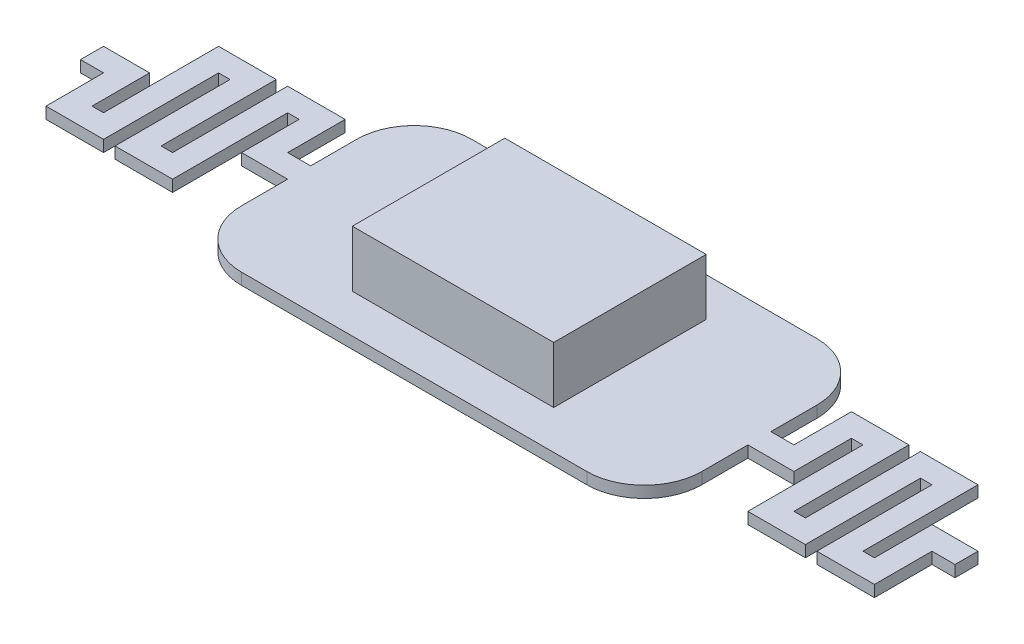
SolidWorks part; units mm, degrees
ref_plane "Front Plane" through (0, 0, 0) normal (0, 0, 1) x (1, 0, 0)
ref_plane "Top Plane" through (0, 0, 0) normal (0, 1, 0) x (1, 0, 0)
ref_plane "Right Plane" through (0, 0, 0) normal (1, 0, 0) x (0, 0, -1)
sketch "Sketch1" plane through (0, 0, 0) normal (0, 1, 0) x (1, 0, 0)
  line L1 (-4, 2) -> (4, 2)
  line L2 (-4, 2) -> (-4, -2)
  line L3 (-4, -2) -> (4, -2)
  line L4 (4, 2) -> (4, -2)
  line L5 (-4, 2) -> (4, -2) construction
  line L6 (-4, -2) -> (4, 2) construction
  point P0 (0, 0)
  dimension "D1" = 8
  dimension "D2" = 4
extrude "Boss-Extrude1" add sketch "Sketch1" along normal blind 0.2
fillet "Fillet1" radius 1 4 edges at (4, 0.1, -2) (4, 0.1, 2) (-4, 0.1, 2) (-4, 0.1, -2)
sketch "Sketch2" plane through (0, 0.2, 0) normal (0, 1, 0) x (1, 0, 0)
  line L0 (4, 0) -> (4.6, 0)
  line L1 (4, -1) -> (4, 1) construction
  line L2 (4.6, 0) -> (4.6, 1)
  line L3 (4.6, 1) -> (5.2, 1)
  line L4 (5.2, 1) -> (5.2, -1)
  line L5 (5.2, -1) -> (5.8, -1)
  line L6 (5.8, -1) -> (5.8, 1)
  line L7 (5.8, 1) -> (6.4, 1)
  line L8 (6.4, 1) -> (6.4, -1)
  line L9 (6.4, -1) -> (7, -1)
  line L10 (7, -1) -> (7, 0)
  line L11 (7, 0) -> (7.6, 0)
  line L12 (4, -0.2) -> (4.8, -0.2)
  line L13 (4.8, -0.2) -> (4.8, 0.8)
  line L14 (4.8, 0.8) -> (5, 0.8)
  line L15 (5, 0.8) -> (5, -1.2)
  line L16 (5, -1.2) -> (6, -1.2)
  line L17 (6, -1.2) -> (6, 0.8)
  line L18 (6, 0.8) -> (6.2, 0.8)
  line L19 (6.2, 0.8) -> (6.2, -1.2)
  line L20 (6.2, -1.2) -> (7.2, -1.2)
  line L21 (7.2, -1.2) -> (7.2, -0.2)
  line L22 (7.2, -0.2) -> (7.6, -0.2)
  line L23 (4, 0.2) -> (4.4, 0.2)
  line L24 (4.4, 0.2) -> (4.4, 1.2)
  line L25 (4.4, 1.2) -> (5.4, 1.2)
  line L26 (5.4, 1.2) -> (5.4, -0.8)
  line L27 (5.4, -0.8) -> (5.6, -0.8)
  line L28 (5.6, -0.8) -> (5.6, 1.2)
  line L29 (5.6, 1.2) -> (6.6, 1.2)
  line L30 (6.6, 1.2) -> (6.6, -0.8)
  line L31 (6.6, -0.8) -> (6.8, -0.8)
  line L32 (6.8, -0.8) -> (6.8, 0.2)
  line L33 (6.8, 0.2) -> (7.6, 0.2)
  line L34 (7.6, 0.2) -> (7.6, -0.2)
  line L35 (4, 0.2) -> (4, -0.2)
  point P5 (5.2, 0)
  point P16 (5.8, 0)
  point P17 (6.4, 0)
  line M12 (4, -1) -> (4, 1)
  dimension "D1" = 2
  dimension "D2" = 0.6
  dimension "D3" = 0.2
  dimension "D4" = 0.2
extrude "Boss-Extrude2" add sketch "Sketch2" against normal up to surface (0.2 mm away) contours L34 L33 L32 L31 L30 L29 L28 L27 L26 L25 L24 L23 L0 L2 L3 L4 L5 L6 L7 L8 L9 L10 L11 M12 | L34 L11 L10 L9 L8 L7 L6 L5 L4 L3 L2 L0 L12 L13 L14 L15 L16 L17 L18 L19 L20 L21 L22 M12 up to face at (0, 0, 0)
mirror "Mirror1" about plane through (0, 0, 0) normal (1, 0, 0) of "Boss-Extrude2"
sketch "Sketch3" plane through (0, 0.2, 0) normal (0, 1, 0) x (1, 0, 0)
  line L1 (-1.75, 1.325) -> (1.75, 1.325)
  line L2 (-1.75, 1.325) -> (-1.75, -1.325)
  line L3 (-1.75, -1.325) -> (1.75, -1.325)
  line L4 (1.75, 1.325) -> (1.75, -1.325)
  line L5 (-1.75, 1.325) -> (1.75, -1.325) construction
  line L6 (-1.75, -1.325) -> (1.75, 1.325) construction
  point P0 (0, 0)
  dimension "D1" = 3.5
  dimension "D2" = 2.65
extrude "Boss-Extrude3" add sketch "Sketch3" along normal blind 0.98
